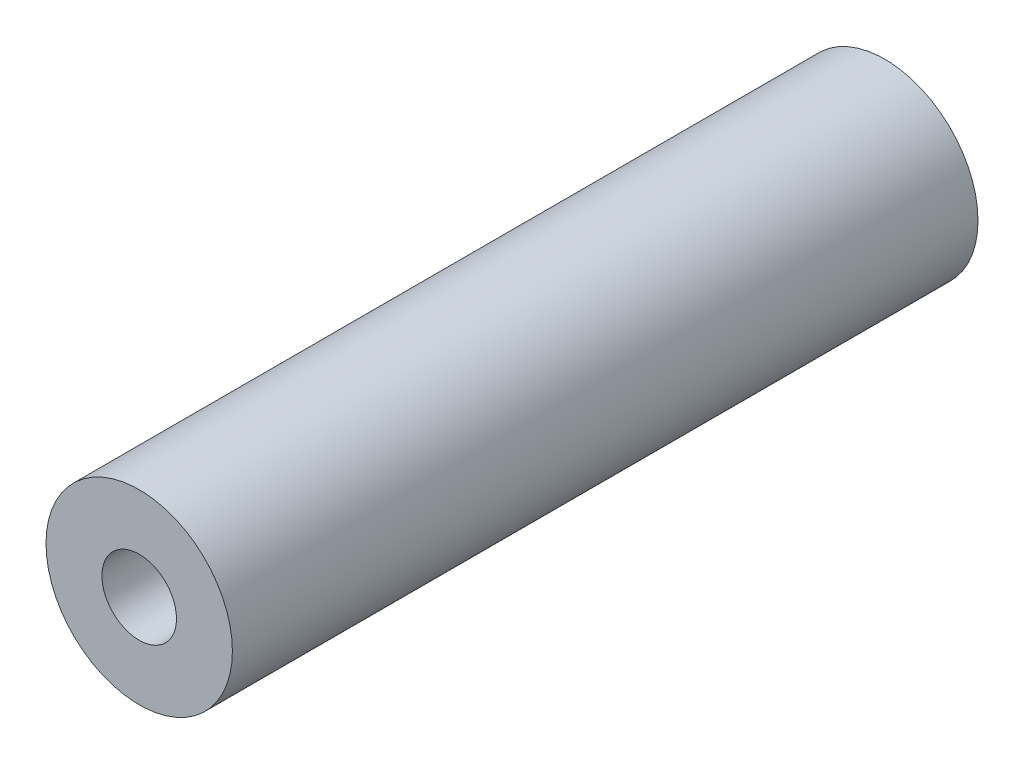
SolidWorks part; units mm, degrees
ref_plane "前基準面" through (0, 0, 0) normal (0, 0, 1) x (1, 0, 0)
ref_plane "上基準面" through (0, 0, 0) normal (0, 1, 0) x (1, 0, 0)
ref_plane "右基準面" through (0, 0, 0) normal (1, 0, 0) x (0, 0, -1)
sketch "草圖1" plane through (0, 0, 0) normal (0, 0, 1) x (1, 0, 0)
  circle A0 centre (0, 0) radius 5
  circle A1 centre (0, 0) radius 2
  dimension "D1" = 10
  dimension "D2" = 4
extrude "填料-伸長1" add sketch "草圖1" along normal blind 40
